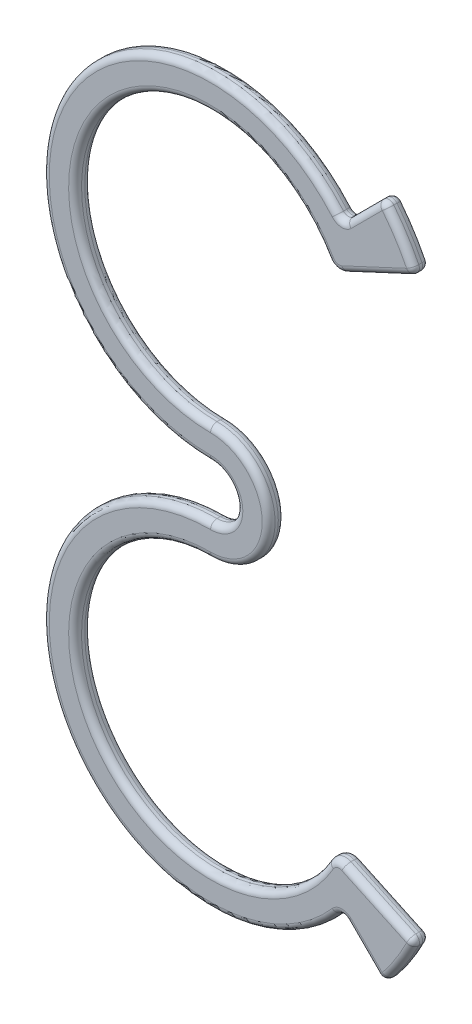
SolidWorks part; units mm, degrees
ref_plane "Front Plane" through (0, 0, 0) normal (0, 0, 1) x (1, 0, 0)
ref_plane "Top Plane" through (0, 0, 0) normal (0, 1, 0) x (1, 0, 0)
ref_plane "Right Plane" through (0, 0, 0) normal (1, 0, 0) x (0, 0, -1)
sketch "Sketch1" plane through (0, 0, 0) normal (0, 0, 1) x (1, 0, 0)
  line L0 (0, 0) -> (0, 17.8979) construction
  line L1 (9.0139, 2.8979) -> (-9.0139, 2.8979) construction
  line L2 (0, 17.8979) -> (15.8604, 25.2938) construction
  line L3 (3.8011, 19.6704) -> (13.347, 29.2164) construction
  line L4 (10.5374, 26.4067) -> (13.347, 29.2164)
  line L5 (10.3831, 22.7396) -> (15.8604, 25.2938)
  line L6 (10.3831, -16.9438) -> (15.8604, -19.4979)
  line L7 (10.5374, -20.6108) -> (13.347, -23.4205)
  circle A0 centre (0, 17.8979) radius 10.5 construction
  circle A1 centre (0, 17.8979) radius 13 construction
  circle A2 centre (0, 17.8979) radius 17.5 construction
  arc A3 (9.8066, 26.432) -> (0, 4.8979) centre (0, 17.8979) ccw
  arc A4 (9.0943, 23.1461) -> (0, 7.3979) centre (0, 17.8979) ccw
  arc A5 (0, 4.8979) -> (0, 0.8979) centre (0, 2.8979) cw
  arc A6 (0, 7.3979) -> (0, -1.6021) centre (0, 2.8979) cw
  arc A7 (13.347, 29.2164) -> (15.8604, 25.2938) centre (0, 17.8979) cw
  arc A8 (9.8066, 26.432) -> (10.5374, 26.4067) centre (10.1838, 26.7602) ccw
  arc A9 (9.0943, 23.1461) -> (10.3831, 22.7396) centre (9.9604, 23.646) ccw
  circle A10 centre (0, -12.1021) radius 13 construction
  circle A11 centre (0, -12.1021) radius 10.5 construction
  arc A12 (9.0943, -17.3502) -> (10.3831, -16.9438) centre (9.9604, -17.8501) cw
  arc A13 (9.8066, -20.6361) -> (10.5374, -20.6108) centre (10.1838, -20.9643) cw
  arc A14 (13.347, -23.4205) -> (15.8604, -19.4979) centre (0, -12.1021) ccw
  arc A15 (9.0943, -17.3502) -> (0, -1.6021) centre (0, -12.1021) cw
  arc A16 (9.8066, -20.6361) -> (0, 0.8979) centre (0, -12.1021) cw
  point P7 (0, 2.8979)
  point P26 (10.1506, 26.0199)
  point P29 (9.5162, 22.3354)
  point P42 (9.5162, -16.5395)
  point P43 (10.1506, -20.224)
  dimension "D2" = 21
  dimension "D4" = 35
  dimension "D8" = 0.5
  dimension "D9" = 1
  dimension "D1" = 15
  dimension "D5" = 65
  dimension "D6" = 20
  dimension "D7" = 13.5
  dimension "D3" = 2.5
extrude "Boss-Extrude1" add sketch "Sketch1" along normal blind 1.25
fillet "Fillet1" radius 0.5 36 edges at (14.7348, 27.3391, 0) (11.9422, 27.8115, 0) (10.1665, 26.2605, 0) (-11.831, 23.2858, 0) (2, 2.8979, 0) (-11.831, -17.4899, 0) (10.1665, -20.4646, 0) (11.9422, -22.0156, 0) (14.7348, -21.5432, 0) (13.1217, -18.2208, 0) (9.6596, -16.8964, 0) (-9.0927, -17.353, 0) (4.5, 2.8979, 0) (-9.0927, 23.1489, 0) (9.6596, 22.6923, 0) (13.1217, 24.0167, 0) (14.7348, 27.3391, 1.25) (11.9422, 27.8115, 1.25) (10.1665, 26.2605, 1.25) (-11.831, 23.2858, 1.25) (2, 2.8979, 1.25) (-11.831, -17.4899, 1.25) (10.1665, -20.4646, 1.25) (11.9422, -22.0156, 1.25) (14.7348, -21.5432, 1.25) (13.1217, -18.2208, 1.25) (9.6596, -16.8964, 1.25) (-9.0927, -17.353, 1.25) (4.5, 2.8979, 1.25) (-9.0927, 23.1489, 1.25) (9.6596, 22.6923, 1.25) (13.1217, 24.0167, 1.25) (15.8604, 25.2938, 0.625) (15.8604, -19.4979, 0.625) (13.347, 29.2164, 0.625) (13.347, -23.4205, 0.625)
